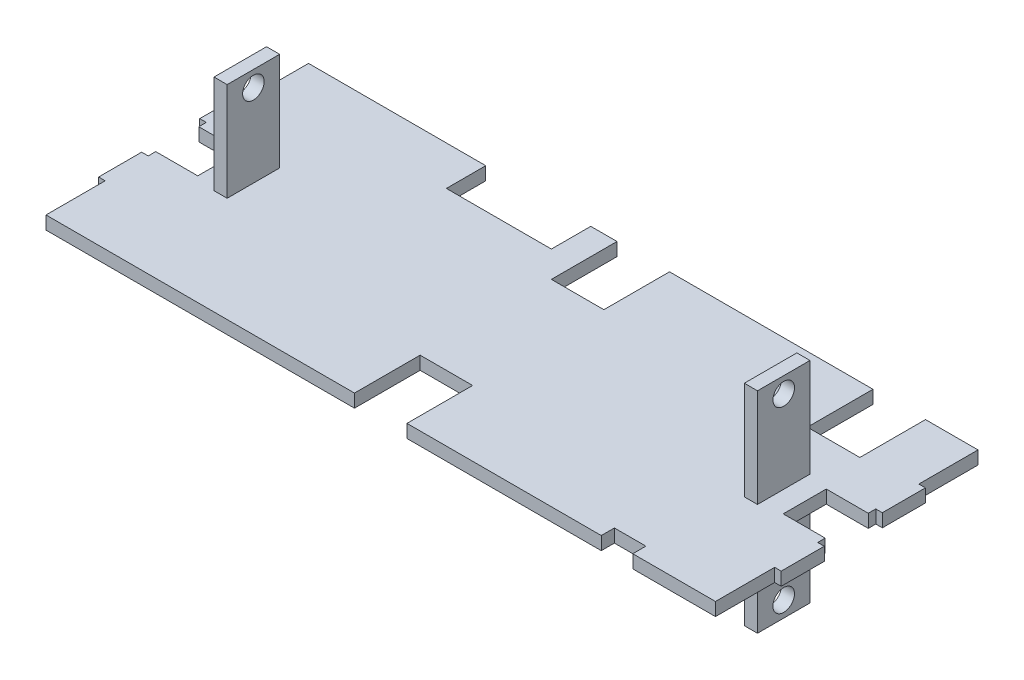
SolidWorks part; units mm, degrees
ref_plane "Front Plane" through (0, 0, 0) normal (0, 0, 1) x (1, 0, 0)
ref_plane "Top Plane" through (0, 0, 0) normal (0, 1, 0) x (1, 0, 0)
ref_plane "Right Plane" through (0, 0, 0) normal (1, 0, 0) x (0, 0, -1)
sketch "Sketch1" plane through (0, 0, 0) normal (0, 1, 0) x (1, 0, 0)
  line L0 (-136.779, 63.5) -> (-111.379, 63.5)
  line L1 (161.925, -63.5) -> (121.92, -63.5)
  line L2 (161.925, -63.5) -> (161.925, -34.8747)
  line L3 (161.925, 63.5) -> (136.525, 63.5)
  line L4 (-161.925, -63.5) -> (-161.925, -34.8747)
  line L5 (161.925, -63.5) -> (-161.925, 63.5) construction
  line L6 (161.925, 63.5) -> (-161.925, -63.5) construction
  line L7 (161.925, 10.414) -> (141.605, 10.414)
  line L9 (161.925, -10.414) -> (141.605, -10.414)
  line L10 (141.605, 10.414) -> (141.605, -10.414)
  line L11 (-136.779, 63.5) -> (-161.925, 63.5)
  line L13 (-161.925, -10.414) -> (-141.605, -10.414)
  line L14 (-141.605, 10.414) -> (-141.605, -10.414)
  line L15 (-161.925, 10.414) -> (-141.605, 10.414)
  line L17 (-141.605, 0) -> (127, 0) construction
  line L18 (-161.925, 14.0467) -> (-165.1, 14.0467)
  line L20 (-161.925, 34.8747) -> (-165.1, 34.8747)
  line L21 (-165.1, 14.0467) -> (-165.1, 34.8747)
  line L22 (-161.925, -34.8747) -> (-165.1, -34.8747)
  line L23 (-165.1, -14.0467) -> (-165.1, -34.8747)
  line L24 (-161.925, -14.0467) -> (-165.1, -14.0467)
  line L27 (161.925, -14.0467) -> (165.1, -14.0467)
  line L28 (165.1, -14.0467) -> (165.1, -34.8747)
  line L29 (161.925, -34.8747) -> (165.1, -34.8747)
  line L30 (161.925, 34.8747) -> (165.1, 34.8747)
  line L31 (165.1, 14.0467) -> (165.1, 34.8747)
  line L32 (161.925, 14.0467) -> (165.1, 14.0467)
  line L34 (-161.925, 34.8747) -> (-161.925, 63.5)
  line L35 (-161.925, -14.0467) -> (-161.925, -10.414)
  line L36 (161.925, 34.8747) -> (161.925, 63.5)
  line L37 (161.925, -14.0467) -> (161.925, -10.414)
  line L38 (-161.925, 10.414) -> (-161.925, 14.0467)
  line L39 (161.925, 10.414) -> (161.925, 14.0467)
  line L44 (111.125, 63.5) -> (111.125, 31.75)
  line L45 (111.125, 31.75) -> (136.525, 31.75)
  line L46 (136.525, 63.5) -> (136.525, 31.75)
  line L47 (111.125, 63.5) -> (12.7, 63.5)
  line L48 (106.68, -63.5) -> (12.7, -63.5)
  line L50 (106.68, -63.5) -> (106.68, -57.15)
  line L51 (106.68, -57.15) -> (121.92, -57.15)
  line L52 (121.92, -63.5) -> (121.92, -57.15)
  line L56 (-135.9408, -63.5) -> (-161.925, -63.5)
  line L57 (-106.68, -63.5) -> (-110.5408, -63.5)
  line L62 (-12.7, 63.5) -> (-111.379, 63.5)
  line L64 (12.7, 63.5) -> (12.7, 31.75)
  line L65 (12.7, 31.75) -> (-12.7, 31.75)
  line L66 (-12.7, 63.5) -> (-12.7, 31.75)
  line L67 (-135.9408, -63.5) -> (-110.5408, -63.5)
  line L68 (12.7, -63.5) -> (12.7, -31.75)
  line L69 (0, 31.75) -> (0, -63.5) construction
  line L70 (12.7, -31.75) -> (-12.7, -31.75)
  line L71 (-12.7, -63.5) -> (-12.7, -31.75)
  line L72 (-12.7, -63.5) -> (-106.68, -63.5)
  point P0 (0, 0)
  point P6 (141.605, 0)
  point P47 (121.92, -60.325)
  point P48 (123.825, 31.75)
  point P50 (0, 63.5)
  point P63 (0, 31.75)
  dimension "D1" = 323.85
  dimension "D2" = 127
  dimension "D3" = 20.828
  dimension "D5" = 3.175
  dimension "D6" = 20.828
  dimension "D4" = 20.32
  dimension "D9" = 25.4
  dimension "D10" = 31.75
  dimension "D13" = 15.24
  dimension "D14" = 6.35
  dimension "D15" = 40.005
  dimension "D11" = 41.275
  dimension "D19" = 31.75
  dimension "D20" = 25.4
  dimension "D7" = 152.4
extrude "Boss-Extrude1" add sketch "Sketch1" along normal mid plane 6.35
sketch "Sketch2" plane through (0, 0, 0) normal (0, 1, 0) x (1, 0, 0)
  line L0 (-141.605, 10.414) -> (-141.605, -10.414) construction
  line L1 (125.095, -12.7) -> (131.445, -12.7)
  line L2 (125.095, -12.7) -> (125.095, 12.7)
  line L3 (125.095, 12.7) -> (131.445, 12.7)
  line L4 (131.445, -12.7) -> (131.445, 12.7)
  line L5 (125.095, -12.7) -> (131.445, 12.7) construction
  line L6 (125.095, 12.7) -> (131.445, -12.7) construction
  line L9 (-125.095, -12.7) -> (-125.095, 12.7)
  line L10 (-125.095, 12.7) -> (-131.445, 12.7)
  line L11 (-131.445, -12.7) -> (-131.445, 12.7)
  line L12 (-125.095, -12.7) -> (-131.445, -12.7)
  line L13 (141.605, -10.414) -> (141.605, 10.414) construction
  point P0 (128.27, 0)
  point P10 (141.605, 0)
  dimension "D1" = 10.16
  dimension "D2" = 10.16
  dimension "D3" = 25.4
  dimension "D4" = 25.4
  dimension "D5" = 6.35
  dimension "D6" = 6.35
  dimension "D7" = 6.35
extrude "Boss-Extrude2" add sketch "Sketch2" along normal mid plane 101.6
sketch "Sketch3" plane through (-131.445, 0, 0) normal (-1, 0, 0) x (0, 0, 1)
  line L0 (-12.7, 50.8) -> (12.7, 50.8) construction
  line L1 (-12.7, -50.8) -> (12.7, -50.8) construction
  circle A0 centre (0, 43.18) radius 5.207
  circle A1 centre (0, -43.18) radius 5.207
  point P4 (0, 50.8)
  dimension "D1" = 10.414
  dimension "D2" = 10.414
  dimension "D3" = 7.62
  dimension "D4" = 7.62
  dimension "D5" = 86.36
extrude "Cut-Extrude1" cut sketch "Sketch3" against normal through all both and the other way through all
sketch "Sketch4" plane through (0, 3.175, 0) normal (0, 1, 0) x (1, 0, 0)
  line L0 (-12.7, 63.5) -> (-161.925, 63.5) construction
  line L1 (-25.4, 63.5) -> (-76.2, 63.5)
  line L2 (-25.4, 63.5) -> (-25.4, 44.45)
  line L3 (-25.4, 44.45) -> (-76.2, 44.45)
  line L4 (-76.2, 63.5) -> (-76.2, 44.45)
  line L5 (-12.7, 31.75) -> (-12.7, 63.5) construction
  dimension "D1" = 50.8
  dimension "D2" = 19.05
  dimension "D3" = 12.7
extrude "Cut-Extrude2" cut sketch "Sketch4" against normal through all
equation "\"length\"= 12.75"
equation "\"width\"=5"
equation "\"height\"= 0.25"
equation "\"D1@Sketch1\"=\"length\""
equation "\"D2@Sketch1\"=\"width\""
equation "\"eyebolt width\"= 0.82"
equation "\"eyebolt length\"= 0.8"
equation "\"D3@Sketch1\"=\"eyebolt width\""
equation "\"D4@Sketch1\"=\"eyebolt length\""
equation "\"lead screw holder height\"= 2.76"
equation "\"lead screw diameter\"=0.41"
equation "\"D1@Sketch3\"=\"lead screw diameter\""
equation "\"distance from holders to board\"=0.4"
equation "\"D2@Sketch3\"=\"lead screw diameter\""
equation "\"lead_screw_dist\"=3.4"
equation "\"D5@Sketch3\"=\"lead_screw_dist\""
